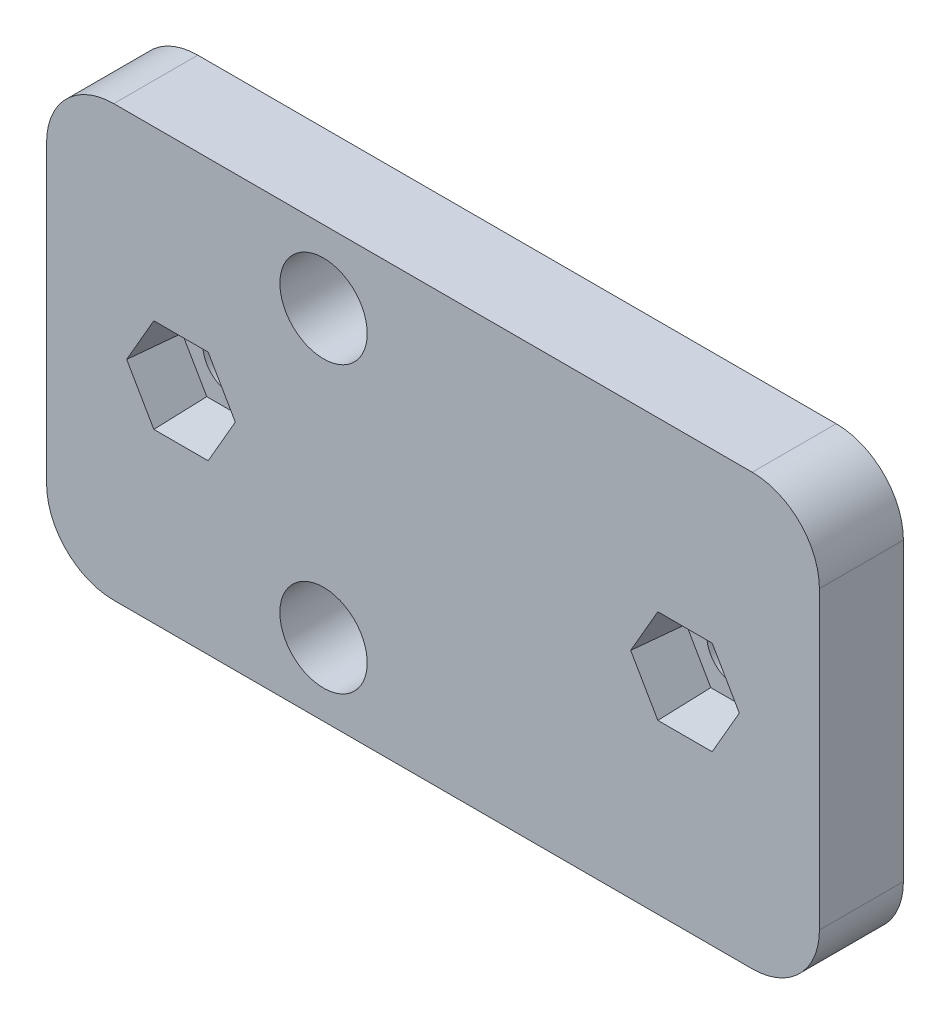
SolidWorks part; units mm, degrees
ref_plane "Plan de face" through (0, 0, 0) normal (0, 0, 1) x (1, 0, 0)
ref_plane "Plan de dessus" through (0, 0, 0) normal (0, 1, 0) x (1, 0, 0)
ref_plane "Plan de droite" through (0, 0, 0) normal (1, 0, 0) x (0, 0, -1)
sketch "Esquisse1" plane through (0, 0, 0) normal (0, 0, 1) x (1, 0, 0)
  line L0 (0.83, 0) -> (9.3153, 8.4853) construction
  line L1 (0.83, 0) -> (3.8892, 0) construction
  line L2 (9.3153, 8.4853) -> (9.3153, -3.4304) construction
  line L3 (15.83, 12.8) -> (15.83, -12.8) construction
  line L4 (-7.17, -12.8) -> (38.83, -12.8)
  line L5 (-7.17, -12.8) -> (-7.17, 12.8)
  line L6 (-7.17, 12.8) -> (38.83, 12.8)
  line L7 (38.83, -12.8) -> (38.83, 12.8)
  line L8 (30.83, 0) -> (30.83, 6.9078) construction
  line L9 (0.83, 0) -> (0.83, 5.9364) construction
  line L10 (38.83, 0) -> (-7.17, 0) construction
  line L11 (0.83, 4.6934) -> (30.83, 4.6934) construction
  line L12 (15.83, 4.6934) -> (15.83, 6.3055) construction
  circle A0 centre (0.83, 0) radius 1.7
  circle A1 centre (9.3153, 8.4853) radius 2.6
  circle A2 centre (9.3153, -8.4853) radius 2.6
  circle A3 centre (30.83, 0) radius 1.7
  circle A4 centre (30.83, 0) radius 7.5 construction
  circle A5 centre (0.83, 0) radius 7.5 construction
  point P12 (9.3153, 0)
  dimension "D1" = 46
  dimension "D3" = 30
  dimension "D2" = 25.6
  dimension "D4" = 0
extrude "Boss.-Extru.1" add sketch "Esquisse1" along normal blind 5
sketch "Esquisse3" plane through (0, 0, 5) normal (0, 0, 1) x (1, 0, 0)
  line L1 (4.0632, 0) -> (2.4466, 2.8)
  line L2 (2.4466, 2.8) -> (-0.7865, 2.8)
  line L3 (-0.7865, 2.8) -> (-2.4031, 0)
  line L4 (-2.4031, 0) -> (-0.7865, -2.8)
  line L5 (-0.7865, -2.8) -> (2.4466, -2.8)
  line L6 (2.4466, -2.8) -> (4.0632, 0)
  line L7 (34.0632, 0) -> (32.4466, 2.8)
  line L8 (32.4466, 2.8) -> (29.2135, 2.8)
  line L9 (29.2135, 2.8) -> (27.5969, 0)
  line L10 (27.5969, 0) -> (29.2135, -2.8)
  line L11 (29.2135, -2.8) -> (32.4466, -2.8)
  line L12 (32.4466, -2.8) -> (34.0632, 0)
  circle A0 centre (0.83, 0) radius 2.8 construction
  circle A1 centre (30.83, 0) radius 2.8 construction
extrude "Enlèv. mat.-Extru.2" cut sketch "Esquisse3" against normal blind 3 draft 5
fillet "Congé1" radius 4 4 edges at (38.83, 12.8, 2.5) (38.83, -12.8, 2.5) (-7.17, -12.8, 2.5) (-7.17, 12.8, 2.5)
